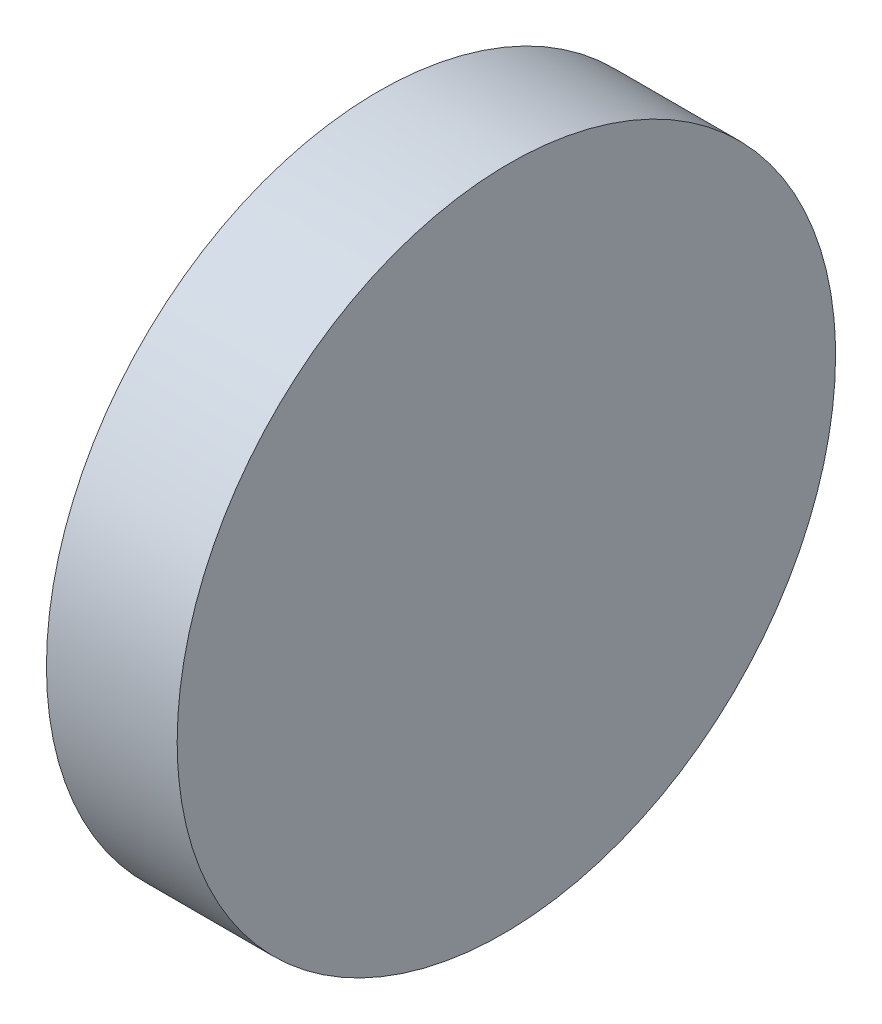
SolidWorks part; units mm, degrees
ref_plane "前视基准面" through (0, 0, 0) normal (0, 0, 1) x (1, 0, 0)
ref_plane "上视基准面" through (0, 0, 0) normal (0, 1, 0) x (1, 0, 0)
ref_plane "右视基准面" through (0, 0, 0) normal (1, 0, 0) x (0, 0, -1)
sketch "草图1" plane through (0, 0, 0) normal (0, 1, 0) x (1, 0, 0)
  line L0 (-12.1202, 0) -> (19.0875, 0) construction
  line L1 (0, 12.7) -> (0, -12.7)
  line L2 (0, -12.7) -> (5, -12.7)
  line L3 (5, -12.7) -> (4.7783, 12.7)
  line L4 (0, 12.7) -> (4.7783, 12.7)
  point P5 (0, 0)
  dimension "D1" = 5
  dimension "D2" = 25.4
  dimension "D3" = 0.5
extrude "凸台-拉伸1" add sketch "草图1" along normal blind 25.4
sketch "草图5" plane through (0, 0, 0) normal (-1, 0, 0) x (0, 0, 1)
  line L0 (0, 0) -> (0, 25.4) construction
  line L1 (-12.7, 25.4) -> (12.7, 25.4) construction
  line L2 (0, 25.4) -> (0.9302, 12.292) construction
  line L3 (-12.7, 12.7) -> (12.7, 12.7) construction
  line L4 (-12.7, 25.4) -> (-12.7, 0) construction
  line L5 (12.7, 25.4) -> (12.7, 0) construction
  line L6 (12.7, 12.7) -> (6.6453, 6.1075) construction
  line L11 (-12.7, 0) -> (12.7, 0)
  line L12 (12.7, 0) -> (12.7, 25.4)
  line L13 (12.7, 25.4) -> (-12.7, 25.4)
  line L14 (-12.7, 25.4) -> (-12.7, 0)
  line L15 (-12.7, 0) -> (12.7, 0)
  line L16 (12.7, 0) -> (12.7, 25.4)
  line L17 (12.7, 25.4) -> (-12.7, 25.4)
  line L18 (-12.7, 25.4) -> (-12.7, 0)
  circle A0 centre (0, 12.7) radius 12.7
  line M5 (-12.7, 0) -> (12.7, 0)
  line M6 (12.7, 0) -> (12.7, 25.4)
  line M7 (12.7, 25.4) -> (-12.7, 25.4)
  line M8 (-12.7, 25.4) -> (-12.7, 0)
  dimension "D1" = 25.4
  dimension "D2" = 0
extrude "切除-拉伸2" cut sketch "草图5" against normal blind 12.5 contours A0 L17 M8 | A0 L18 M5 | A0 L15 M6 | A0 L16 M7
